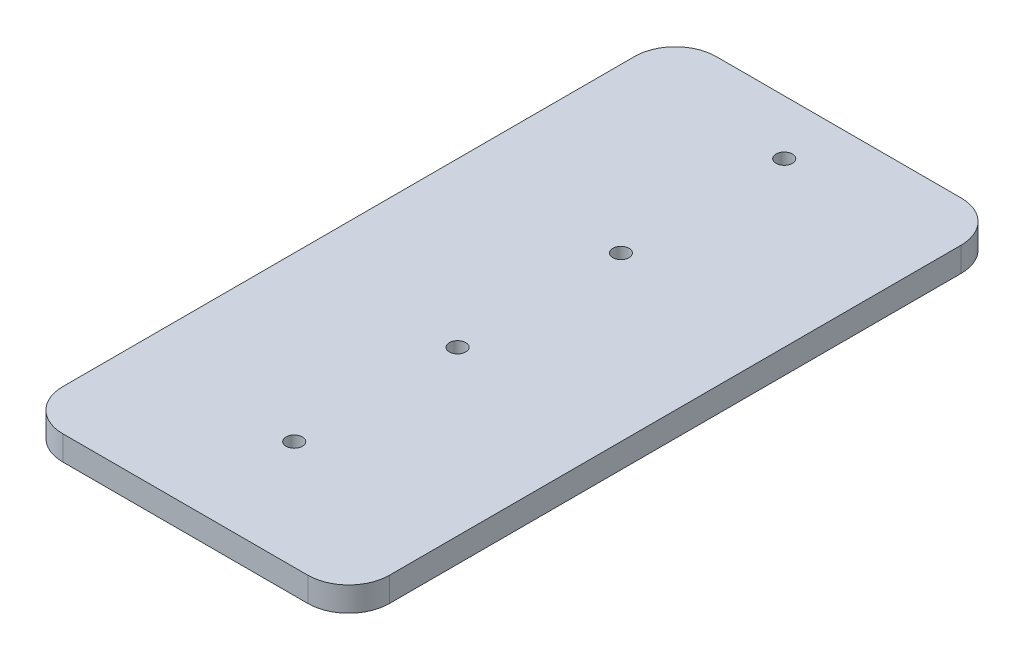
SolidWorks part; units mm, degrees
ref_plane "Front Plane" through (0, 0, 0) normal (0, 0, 1) x (1, 0, 0)
ref_plane "Top Plane" through (0, 0, 0) normal (0, 1, 0) x (1, 0, 0)
ref_plane "Right Plane" through (0, 0, 0) normal (1, 0, 0) x (0, 0, -1)
sketch "Sketch1" plane through (0, 0, 0) normal (0, 1, 0) x (1, 0, 0)
  line L1 (-27, -27) -> (-27, -47)
  line L2 (-17, -57) -> (43, -57)
  line L3 (53, -47) -> (53, -27)
  line L5 (-17, 103) -> (43, 103)
  line L6 (-27, 93) -> (-27, -27)
  line L8 (53, 93) -> (53, -27)
  circle A0 centre (13, 89.6667) radius 2
  circle A1 centre (13, 49.6667) radius 2
  circle A2 centre (13, 9.6667) radius 2
  circle A3 centre (13, -30.3333) radius 2
  arc A4 (-27, -47) -> (-17, -57) centre (-17, -47) ccw
  arc A5 (43, -57) -> (53, -47) centre (43, -47) ccw
  arc A6 (53, 93) -> (43, 103) centre (43, 93) ccw
  arc A7 (-27, 93) -> (-17, 103) centre (-17, 93) cw
  dimension "D1" = 10
  dimension "D3" = 40
  dimension "D4" = 40
  dimension "D5" = 40
  dimension "D8" = 4
  dimension "D9" = 4
  dimension "D6" = 4
  dimension "D7" = 4
extrude "Boss-Extrude1" add sketch "Sketch1" along normal blind 6
scale "Scale1" scale about centroid uniform scaling yes scale factor 7.5
